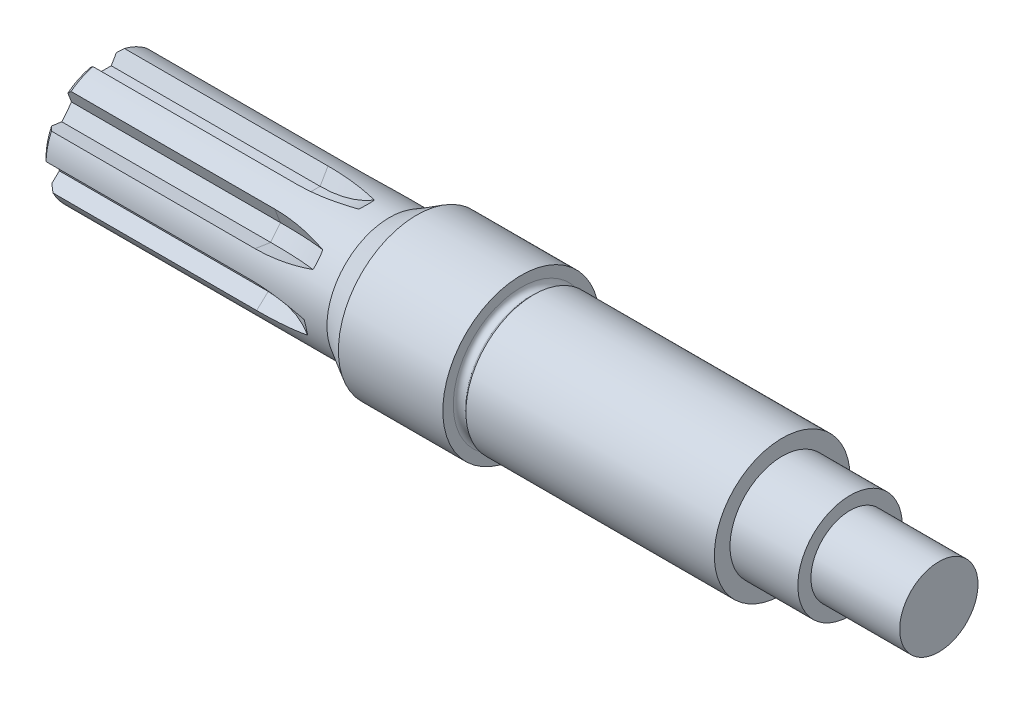
SolidWorks part; units mm, degrees
ref_plane "Přední rovina" through (0, 0, 0) normal (0, 0, 1) x (1, 0, 0)
ref_plane "Horní rovina" through (0, 0, 0) normal (0, 1, 0) x (1, 0, 0)
ref_plane "Pravá rovina" through (0, 0, 0) normal (1, 0, 0) x (0, 0, -1)
sketch "Skica1" plane through (0, 0, 0) normal (0, 0, 1) x (1, 0, 0)
  line L0 (-80, 2.5) -> (-61.4434, 2.5)
  line L1 (-61.4434, 2.5) -> (-60, 0)
  line L2 (-60, 0) -> (80, 0)
  line L3 (80, 0) -> (80, 7.5)
  line L4 (80, 7.5) -> (63, 7.5)
  line L5 (63, 7.5) -> (63, 10)
  line L6 (63, 10) -> (50, 10)
  line L7 (50, 10) -> (50, 13)
  line L8 (50, 13) -> (2.4142, 13)
  line L9 (2.4142, 13) -> (1.7071, 12.2929)
  line L10 (0, 13) -> (0, 15)
  line L11 (0, 15) -> (-20, 15)
  line L12 (-20, 15) -> (-25.1962, 12)
  line L13 (-25.1962, 12) -> (-79, 12)
  line L14 (-79, 12) -> (-80, 11)
  line L15 (-80, 11) -> (-80, 2.5)
  line L16 (89.4902, 0) -> (-36.1523, 0) construction
  arc A0 (1.7071, 12.2929) -> (0, 13) centre (1, 13) cw
  arc A1 (-79, 12) -> (-80, 11) centre (-79, 11) ccw construction
  dimension "D5" = 1
  dimension "D9" = 24
  dimension "D10" = 1
  dimension "D1" = 5
  dimension "D2" = 60
  dimension "D3" = 20
  dimension "D4" = 24
  dimension "D6" = 30
  dimension "D7" = 30
  dimension "D8" = 26
  dimension "D11" = 45
  dimension "D12" = 20
  dimension "D13" = 80
  dimension "D14" = 20
  dimension "D15" = 15
  dimension "D16" = 17
  dimension "D17" = 30
  dimension "D18" = 80
revolve "Rotovat1" add sketch "Skica1" angle 360 about L16
sketch "Skica2" plane through (0, 0, 0) normal (0, 0, 1) x (1, 0, 0)
  line L0 (-80, 9) -> (-40, 9)
  line L1 (-80, 11) -> (-80, -11) construction
  arc A0 (-40, 9) -> (-22.7075, 18.9517) centre (-40, 29) ccw
  dimension "D2" = 20
  dimension "D1" = 9
  dimension "D3" = 40
sketch "Skica3" plane through (-80, 0, 0) normal (-1, 0, 0) x (0, 0, 1)
  line L0 (-4.1682, 13.6214) -> (-1.5, 9)
  line L1 (-1.5, 9) -> (1.5, 9)
  line L2 (1.5, 9) -> (4.1682, 13.6214)
  line L3 (0, 13.8145) -> (0, 9) construction
  line L4 (-4.1682, 13.6214) -> (4.1682, 13.6214)
  dimension "D1" = 3
  dimension "D2" = 60
sweep "Odebrat tažením po křivce1" cut profiles "Skica3" path "Skica2"
pattern_circular "Kruhové pole1" count 7 over 360 about axis through (0, 0, 0) along (1, 0, 0) of "Odebrat tažením po křivce1"
